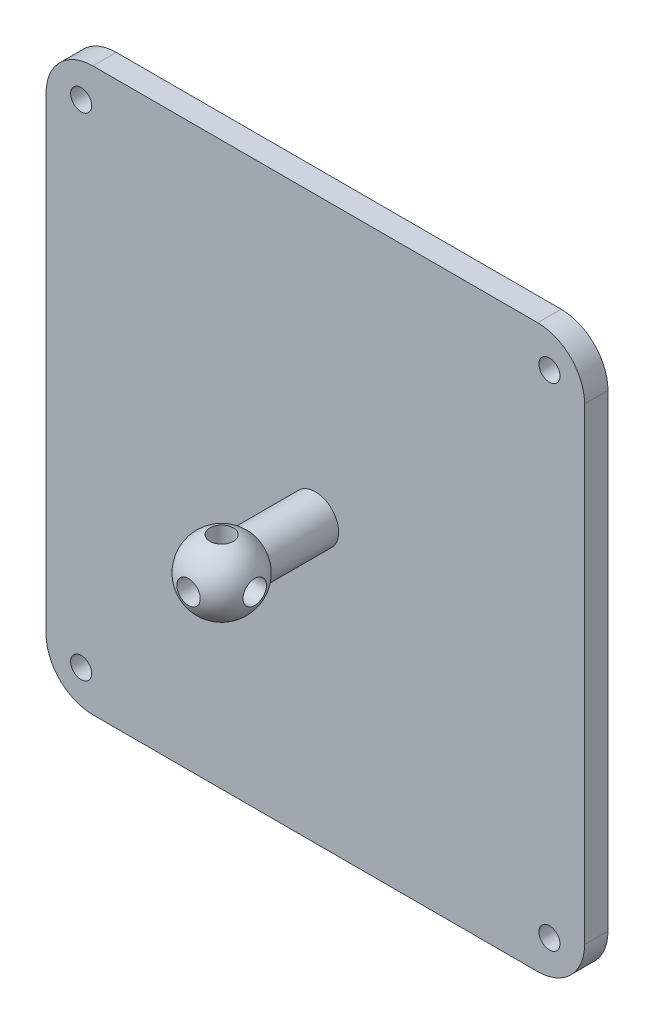
SolidWorks part; units mm, degrees
ref_plane "Front Plane" through (0, 0, 0) normal (0, 0, 1) x (1, 0, 0)
ref_plane "Top Plane" through (0, 0, 0) normal (0, 1, 0) x (1, 0, 0)
ref_plane "Right Plane" through (0, 0, 0) normal (1, 0, 0) x (0, 0, -1)
sketch "Sketch2" plane through (0, 0, 0) normal (0, 0, 1) x (1, 0, 0)
  line L0 (0, 75.1747) -> (0, -38.0296) construction
  line L1 (-57.5, 60) -> (57.5, 60)
  line L2 (-57.5, 60) -> (-57.5, -60)
  line L3 (-57.5, -60) -> (57.5, -60)
  line L4 (57.5, 60) -> (57.5, -60)
  line L5 (0, -55) -> (0, 55) construction
  line L7 (-49.2865, 0) -> (47.6124, 0) construction
  line L8 (55, 0) -> (-55, 0) construction
  circle A0 centre (50, 52.5) radius 2.25
  circle A1 centre (50, -52.5) radius 2.25
  circle A2 centre (-50, -52.5) radius 2.25
  circle A3 centre (-50, 52.5) radius 2.25
  dimension "D4" = 4.5
  dimension "D1" = 120
  dimension "D2" = 115
  dimension "D3" = 52.5
  dimension "D5" = 50
extrude "Boss-Extrude1" add sketch "Sketch2" against normal blind 5
sketch "Sketch3" plane through (0, 0, 0) normal (0, 0, 1) x (1, 0, 0)
  circle A0 centre (0, 0) radius 5
  dimension "D1" = 10
extrude "Boss-Extrude2" add sketch "Sketch3" along normal blind 20
sketch "Sketch4" plane through (0, 0, 0) normal (0, 1, 0) x (1, 0, 0)
  line L0 (-5, -20) -> (5, -20)
  line L1 (-5, -20) -> (5, -20) construction
  line L2 (0, 22.8868) -> (0, -4.1933) construction
  line L3 (0, -12.5) -> (0, -27.5)
  arc A0 (0, -27.5) -> (0, -12.5) centre (0, -20) ccw
  dimension "D1" = 15
revolve "Revolve3" add sketch "Sketch4" angle 360 about L2
sketch "Sketch6" plane through (0, 0, 0) normal (1, 0, 0) x (0, 0, -1)
  line L0 (-20, 42.1775) -> (-20, -42.1775) construction
  line L3 (-20, 15) -> (-17.5, 15)
  line L4 (-20, 15) -> (-20, -3)
  line L5 (-20, -3) -> (-17.5, -3)
  line L6 (-17.5, 15) -> (-17.5, -3)
  arc A0 (-14.4098, 5) -> (-14.4098, -5) centre (-20, 0) ccw
  arc A1 (-14.4098, 5) -> (-14.4098, -5) centre (-20, 0) ccw construction
  dimension "D1" = 2.5
  dimension "D2" = 3
  dimension "D3" = 15
revolve "Cut-Revolve1" cut sketch "Sketch6" angle 360 about L0
sketch "Sketch8" plane through (0, 0, 0) normal (1, 0, 0) x (0, 0, -1)
  line L0 (-46.426, 0) -> (22.2133, 0) construction
  line L2 (-35, 2.5) -> (-17, 2.5)
  line L3 (-35, 2.5) -> (-35, 0)
  line L4 (-35, 0) -> (-17, 0)
  line L5 (-17, 2.5) -> (-17, 0)
  arc A0 (-22.5, 7.0711) -> (-14.4098, -5) centre (-20, 0) ccw
  arc A1 (-4.4098, 5) -> (-7.5, 7.0711) centre (-10, 0) ccw
  arc A3 (-22.5, 7.0711) -> (-14.4098, -5) centre (-20, 0) ccw construction
  dimension "D1" = 3
  dimension "D2" = 2.5
  dimension "D3" = 15
revolve "Cut-Revolve2" cut sketch "Sketch8" angle 360 about L0
sketch "Sketch9" plane through (0, 0, 0) normal (0, 1, 0) x (1, 0, 0)
  line L0 (-16.0302, -20) -> (16.0302, -20) construction
  line L2 (15, -17.5) -> (-3, -17.5)
  line L3 (15, -17.5) -> (15, -20)
  line L4 (15, -20) -> (-3, -20)
  line L5 (-3, -17.5) -> (-3, -20)
  arc A0 (-5, -14.4098) -> (-2.5, -27.0711) centre (0, -20) ccw
  arc A1 (2.5, -27.0711) -> (5, -14.4098) centre (0, -20) ccw
  arc A2 (2.5, -27.0711) -> (5, -14.4098) centre (0, -20) ccw construction
  arc A3 (-5, -14.4098) -> (-2.5, -27.0711) centre (0, -20) ccw construction
  dimension "D1" = 3
  dimension "D2" = 15
  dimension "D3" = 2.5
revolve "Cut-Revolve3" cut sketch "Sketch9" angle 360 about L0
fillet "Fillet1" radius 10 4 edges at (57.5, 60, -2.5) (-57.5, 60, -2.5) (57.5, -60, -2.5) (-57.5, -60, -2.5)
equation "\"D1@Sketch8\"=\"D2@Sketch6\""
equation "\"D3@Sketch8\"=\"D3@Sketch6\""
equation "\"D2@Sketch8\"=\"D1@Sketch6\""
equation "\"D1@Sketch9\"=\"D2@Sketch6\""
equation "\"D2@Sketch9\"=\"D3@Sketch6\""
equation "\"D3@Sketch9\"=\"D1@Sketch6\""
